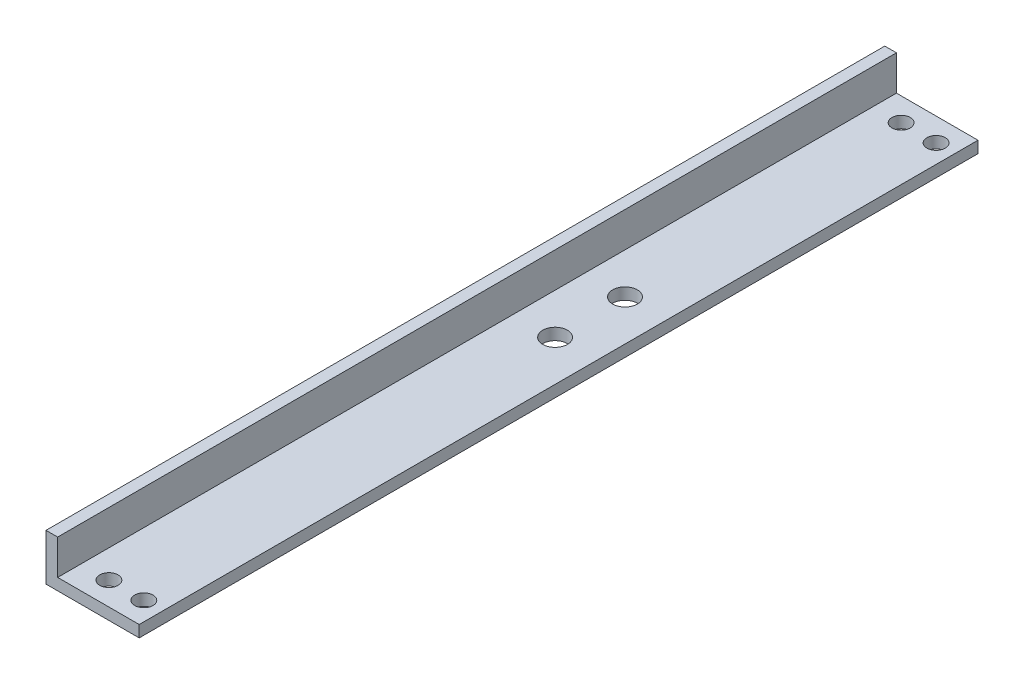
SolidWorks part; units mm, degrees
material "6061-T6 (SS)"
ref_plane "Front Plane" through (0, 0, 0) normal (0, 0, 1) x (1, 0, 0)
ref_plane "Top Plane" through (0, 0, 0) normal (0, 1, 0) x (1, 0, 0)
ref_plane "Right Plane" through (0, 0, 0) normal (1, 0, 0) x (0, 0, -1)
sketch "Sketch1" plane through (0, 0, 0) normal (0, 0, 1) x (1, 0, 0)
  line L0 (0, 0) -> (0, 25.4)
  line L1 (0, 0) -> (25.4, 0)
  line L2 (25.4, 0) -> (25.4, 3.175)
  line L3 (25.4, 3.175) -> (3.175, 3.175)
  line L4 (3.175, 3.175) -> (3.175, 25.4)
  line L5 (3.175, 25.4) -> (0, 25.4)
  dimension "D1" = 25.4
  dimension "D2" = 25.4
  dimension "D3" = 3.175
  dimension "D4" = 3.175
extrude "Boss-Extrude1" add sketch "Sketch1" along normal blind 228.6
sketch "Sketch2" plane through (0, 3.175, 0) normal (0, 1, 0) x (1, 0, 0)
  line L1 (25.4, -228.6) -> (25.4, 0) construction
  line L3 (25.4, -114.3) -> (-22.9586, -114.3) construction
  line L5 (3.175, -228.6) -> (3.175, 0) construction
  line L6 (25.4, -228.6) -> (3.175, -228.6) construction
  circle A4 centre (20.32, -222.25) radius 2.4892
  circle A5 centre (10.795, -222.25) radius 2.4892
  circle A6 centre (20.32, -6.35) radius 2.4892
  circle A7 centre (10.795, -6.35) radius 2.4892
  dimension "D1" = 4.9784
  dimension "D4" = 7.62
  dimension "D6" = 6.35
  dimension "D3" = 4.9784
  dimension "D2" = 5.08
  dimension "D5" = 6.35
extrude "Cut-Extrude1" cut sketch "Sketch2" against normal through all
sketch "Sketch3" plane through (3.175, 0, 0) normal (1, 0, 0) x (0, 0, -1)
  line L0 (-228.6, 25.4) -> (0, 25.4) construction
  line L1 (-228.6, 25.4) -> (0, 25.4)
  line L2 (-228.6, 25.4) -> (-228.6, 12.7)
  line L3 (-228.6, 12.7) -> (0, 12.7)
  line L4 (0, 25.4) -> (0, 12.7)
  line L5 (-228.6, 3.175) -> (0, 3.175) construction
  line L8 (0, 3.175) -> (0, 25.4) construction
  line L9 (-228.6, 25.4) -> (-228.6, 0) construction
  dimension "D2" = 9.525
extrude "Cut-Extrude2" cut sketch "Sketch3" against normal through all
sketch "Sketch4" plane through (0, 3.175, 0) normal (0, 1, 0) x (1, 0, 0)
  line L0 (3.175, -75.565) -> (1132.6648, -75.565) construction
  line L1 (3.175, -228.6) -> (3.175, 0) construction
  line L2 (1041.4, -75.565) -> (1104.9, -75.565) construction
  line L3 (3.175, -113.665) -> (56.6409, -113.665) construction
  line L4 (14.2875, -85.09) -> (25.4, -85.09) construction
  line L5 (25.4, -228.6) -> (25.4, 0) construction
  line L6 (14.2875, -85.09) -> (3.175, -85.09) construction
  circle A0 centre (14.2875, -104.14) radius 3.3655
  circle A1 centre (14.2875, -85.09) radius 3.3655
  dimension "D2" = 6.731
  dimension "D1" = 19.05
  dimension "D3" = 38.1
  dimension "D4" = 9.525
extrude "Cut-Extrude3" cut sketch "Sketch4" against normal through all contours A1 | A0
equation "\"D4@Sketch4\"=(\"D3@Sketch4\"-\"D1@Sketch4\")/2"
